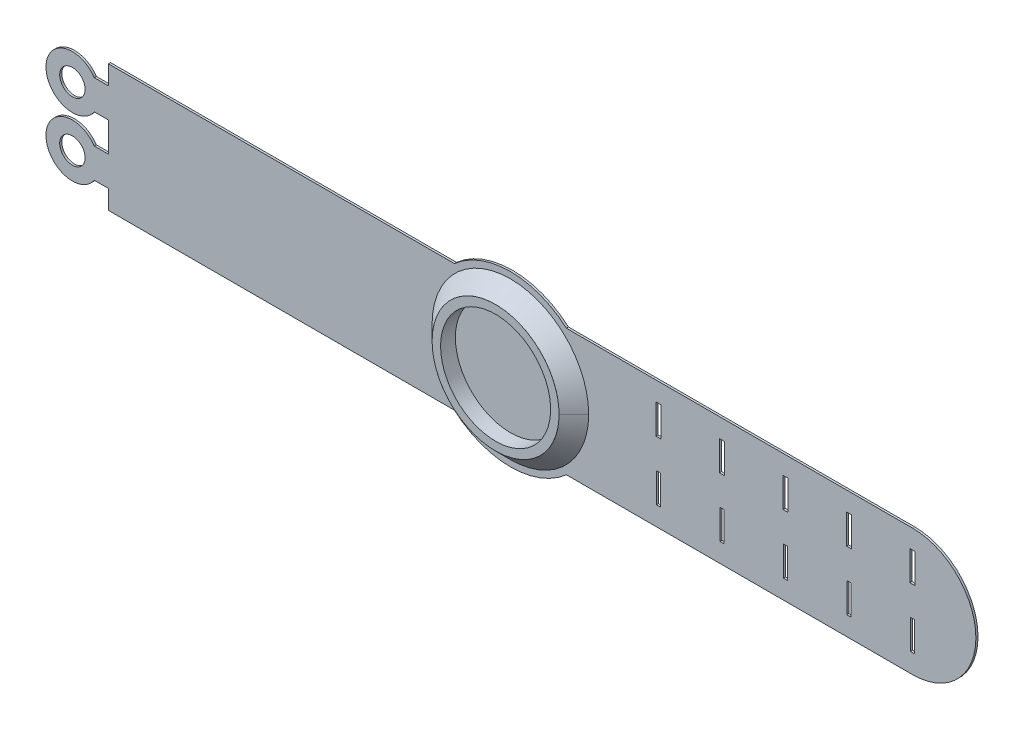
SolidWorks part; units mm, degrees
ref_plane "Спереди" through (0, 0, 0) normal (0, 0, 1) x (1, 0, 0)
ref_plane "Сверху" through (0, 0, 0) normal (0, 1, 0) x (1, 0, 0)
ref_plane "Справа" through (0, 0, 0) normal (1, 0, 0) x (0, 0, -1)
sketch "Эскиз1" plane through (0, 0, 0) normal (0, 0, 1) x (1, 0, 0)
  line L0 (13.2288, 15) -> (95, 15)
  line L1 (-95, 15) -> (-13.2288, 15)
  line L3 (-95, -15) -> (-13.2288, -15)
  line L5 (-95, 15) -> (95, -15) construction
  line L6 (-95, -15) -> (95, 15) construction
  line L7 (13.2288, -15) -> (95, -15)
  line L8 (-95, 15) -> (-95, -15)
  line L9 (80.6, 10.5) -> (80.6, 3.5)
  line L10 (-98.3219, 10.5) -> (-95, 10.5)
  line L12 (-98.3219, 3.5) -> (-95, 3.5)
  line L13 (-95, 10.5) -> (-95, 3.5)
  line L14 (-99.9506, 11.201) -> (-95, 3.5) construction
  line L15 (-99.0084, 4.2647) -> (-95, 10.5) construction
  line L16 (-98.3219, -3.5) -> (-95, -3.5)
  line L18 (-98.3219, -10.5) -> (-95, -10.5)
  line L19 (-95, -3.5) -> (-95, -10.5)
  line L20 (-99.0084, -4.2647) -> (-95, -10.5) construction
  line L21 (-99.9506, -11.201) -> (-95, -3.5) construction
  line L22 (95.6, 10.5) -> (94.4, 10.5)
  line L23 (95.6, 10.5) -> (95.6, 3.5)
  line L24 (95.6, 3.5) -> (94.4, 3.5)
  line L25 (94.4, 10.5) -> (94.4, 3.5)
  line L26 (95.6, 10.5) -> (94.4, 3.5) construction
  line L27 (95.6, 3.5) -> (94.4, 10.5) construction
  line L28 (95.5, -3.5) -> (94.5, -3.5)
  line L29 (95.5, -3.5) -> (95.5, -10.5)
  line L30 (95.5, -10.5) -> (94.5, -10.5)
  line L31 (94.5, -3.5) -> (94.5, -10.5)
  line L32 (95.5, -3.5) -> (94.5, -10.5) construction
  line L33 (95.5, -10.5) -> (94.5, -3.5) construction
  line L34 (80.6, 10.5) -> (79.4, 10.5)
  line L35 (79.4, 10.5) -> (79.4, 3.5)
  line L36 (80.6, 3.5) -> (79.4, 3.5)
  line L37 (80.5, -3.5) -> (79.5, -3.5)
  line L38 (80.5, -3.5) -> (80.5, -10.5)
  line L39 (79.5, -3.5) -> (79.5, -10.5)
  line L40 (80.5, -10.5) -> (79.5, -10.5)
  line L41 (65.6, 10.5) -> (65.6, 3.5)
  line L42 (65.6, 10.5) -> (64.4, 10.5)
  line L43 (64.4, 10.5) -> (64.4, 3.5)
  line L44 (65.6, 3.5) -> (64.4, 3.5)
  line L45 (65.5, -3.5) -> (64.5, -3.5)
  line L46 (65.5, -3.5) -> (65.5, -10.5)
  line L47 (64.5, -3.5) -> (64.5, -10.5)
  line L48 (65.5, -10.5) -> (64.5, -10.5)
  line L49 (50.6, 10.5) -> (50.6, 3.5)
  line L50 (50.6, 10.5) -> (49.4, 10.5)
  line L51 (49.4, 10.5) -> (49.4, 3.5)
  line L52 (50.6, 3.5) -> (49.4, 3.5)
  line L53 (50.5, -3.5) -> (49.5, -3.5)
  line L54 (50.5, -3.5) -> (50.5, -10.5)
  line L55 (49.5, -3.5) -> (49.5, -10.5)
  line L56 (50.5, -10.5) -> (49.5, -10.5)
  line L57 (34.5, -3.5) -> (34.5, -10.5)
  line L58 (35.5, -3.5) -> (35.5, -10.5)
  line L59 (35.5, -10.5) -> (34.5, -10.5)
  line L60 (35.5, -3.5) -> (34.5, -3.5)
  line L61 (35.6, 3.5) -> (34.4, 3.5)
  line L62 (35.6, 10.5) -> (35.6, 3.5)
  line L63 (34.4, 10.5) -> (34.4, 3.5)
  line L64 (35.6, 10.5) -> (34.4, 10.5)
  line L73 (20.5, -3.5) -> (20.5, -10.5) [skipped]
  line L74 (20.5, -10.5) -> (19.5, -10.5) [skipped]
  line L75 (20.5, -3.5) -> (19.5, -3.5) [skipped]
  line L76 (19.4, 10.5) -> (19.4, 3.5) [skipped]
  line L77 (20.6, 10.5) -> (20.6, 3.5) [skipped]
  line L78 (20.6, 3.5) -> (19.4, 3.5) [skipped]
  line L79 (20.6, 10.5) -> (19.4, 10.5) [skipped]
  line L80 (19.5, -3.5) -> (19.5, -10.5) [skipped]
  arc A0 (13.2288, 15) -> (-13.2288, 15) centre (0, 0) ccw
  arc A1 (95, -15) -> (95, 15) centre (95, 0) ccw
  arc A2 (-13.2288, -15) -> (13.2288, -15) centre (0, 0) ccw
  arc A3 (-98.3219, 10.5) -> (-98.3219, 3.5) centre (-103.5, 7) ccw
  arc A4 (-98.3219, -3.5) -> (-98.3219, -10.5) centre (-103.5, -7) ccw
  circle A5 centre (-103.5, 7) radius 3
  circle A6 centre (-103.5, -7) radius 3
  point P0 (0, 0)
  point P11 (-97.25, 7)
  point P17 (-97.25, -7)
  point P23 (-96.661, 3.5)
  point P26 (-96.661, -3.5)
  point P32 (95, 7)
  point P37 (95, -7)
  dimension "D3" = 40
  dimension "D4" = 20
  dimension "D5" = 0
  dimension "D6" = 5
  dimension "D12" = 12.5
  dimension "D13" = 12.5
  dimension "D16" = 6
  dimension "D17" = 6
  dimension "D18" = 8.5
  dimension "D21" = 8.5
  dimension "D1" = 190
  dimension "D2" = 30
  dimension "D7" = 5
  dimension "D8" = 8
  dimension "D9" = 8
  dimension "D10" = 7
  dimension "D11" = 7
  dimension "D14" = 8
  dimension "D15" = 8
  dimension "D19" = 4.5
  dimension "D20" = 11.5
  dimension "D22" = 4.5
  dimension "D23" = 18.5
  dimension "D24" = 8
  dimension "D25" = 8
  dimension "D26" = 7
  dimension "D27" = 7
  dimension "D28" = 1.2
  dimension "D29" = 1
  dimension "D31" = 14.4
  dimension "D33" = 14
  dimension "D30" = 4
  dimension "D32" = 3
extrude "Бобышка-Вытянуть2" add sketch "Эскиз1" along normal blind 0.5 contours L10 A3 L12 L8 A5 | L3 A2 L7 A1 L0 A0 L1 L8 L54 L56 L55 L53 L49 L52 L51 L50 L46 L48 L47 L45 L41 L44 L43 L42 L38 L40 L39 L37 L9 L36 L35 L34 L25 L22 L23 L24 L31 L28 L29 | L16 A4 L18 L8 A6
sketch "Эскиз3" plane through (0, 0, 0) normal (0, 0, -1) x (-1, 0, 0)
  circle A0 centre (0, 0) radius 13
  circle A1 centre (0, 0) radius 15
  dimension "D1" = 26
  dimension "D2" = 30
extrude "Бобышка-Вытянуть3" add sketch "Эскиз3" against normal blind 4
sketch3d "Трехмерный эскиз1"
  line L0 (15, 0, 0.5) -> (18.5, 0, 0.5)
  line L1 (15, 0, 4) -> (18.5, 0, 0.5)
  line L2 (15, 0, 4) -> (15, 0, 0.5)
  circle A0 centre (0, 0, 0.5) radius 15 construction
  circle A1 centre (0, 0, 4) radius 15 construction
  point P4 (0, 0, 15.5)
  point P9 (0, 0, -11)
  dimension "D1" = 45
sketch "Эскиз7" plane through (0, 0, 0) normal (0, 0, -1) x (-1, 0, 0)
surface "Поверхность-По траектории1"
sketch3d "Трехмерный эскиз2"
  line L0 (-15, 0, 4) -> (15, 0, 4) construction
  line L1 (0, -15, 4) -> (0, 15, 4) construction
  line L2 (-10.6066, -10.6066, 4) -> (10.6066, 10.6066, 4) construction
  line L3 (10.6066, -10.6066, 4) -> (-10.6066, 10.6066, 4) construction
  line L4 (-13.8582, -5.7403, 4) -> (13.8582, 5.7403, 4) construction
  line L5 (-5.7403, -13.8582, 4) -> (5.7403, 13.8582, 4) construction
  line L6 (-13.8582, 5.7403, 4) -> (13.8582, -5.7403, 4) construction
  line L7 (5.7403, -13.8582, 4) -> (-5.7403, 13.8582, 4) construction
  line L8 (13.8582, -5.7403, 4) -> (17.0918, -7.0796, 0.5)
  line L9 (13.8582, 5.7403, 4) -> (17.0918, 7.0796, 0.5)
  line L10 (17.0918, -7.0796, 0.5) -> (18.9395, -7.845, 0.5)
  line L11 (13.8582, -5.7403, 4) -> (15.706, -6.5056, 4)
  line L12 (15.706, -6.5056, 4) -> (18.9395, -7.845, 0.5)
  line L13 (17.0918, 7.0796, 0.5) -> (18.9395, 7.845, 0.5)
  line L14 (13.8582, 5.7403, 4) -> (15.706, 6.5056, 4)
  line L15 (15.706, 6.5056, 4) -> (18.9395, 7.845, 0.5)
  line L17 (-17.0918, -7.0796, 0.5) -> (-18.9395, -7.845, 0.5)
  line L18 (-13.8582, -5.7403, 4) -> (-17.0918, -7.0796, 0.5)
  line L19 (-15.706, -6.5056, 4) -> (-18.9395, -7.845, 0.5)
  line L20 (-17.0918, 7.0796, 0.5) -> (-18.9395, 7.845, 0.5)
  line L21 (-13.8582, 5.7403, 4) -> (-15.706, 6.5056, 4)
  line L22 (-13.8582, 5.7403, 4) -> (-17.0918, 7.0796, 0.5)
  line L23 (-15.706, 6.5056, 4) -> (-18.9395, 7.845, 0.5)
  line L24 (-13.8582, -5.7403, 4) -> (-15.706, -6.5056, 4)
  circle A0 centre (0, 0, 4) radius 15 construction
  arc A1 (-15, 0, 4) -> (15, 0, 4) centre (0, 0, 4) ccw construction
  arc A2 (15, 0, 4) -> (-15, 0, 4) centre (0, 0, 4) ccw construction
  arc A3 (-18.5, 0, 0.5) -> (18.5, 0, 0.5) centre (0, 0, 0.5) ccw construction
  arc A4 (18.5, 0, 0.5) -> (-18.5, 0, 0.5) centre (0, 0, 0.5) ccw construction
  arc A5 (-15.706, 6.5056, 4) -> (-15.706, -6.5056, 4) centre (0, 0, 4) ccw
  arc A6 (15.706, -6.5056, 4) -> (15.706, 6.5056, 4) centre (0, 0, 4) ccw
  point P8 (0, 0, -11)
  point P12 (0, 0, 19)
  point P16 (0, 0, 19)
  point P19 (0, 0, 4)
  point P34 (0, 0, 19)
  point P40 (0, 0, 19)
  point P52 (0, 0, 21)
  point P53 (0, 0, 21)
  dimension "D2" = 22.5
  dimension "D3" = 22.5
  dimension "D4" = 22.5
  dimension "D5" = 22.5
  dimension "D6" = 22.5
  dimension "D7" = 135
  dimension "D8" = 135
  dimension "D9" = 2
sketch "Эскиз24" plane through (0, 0, 0.5) normal (0, 0, 1) x (1, 0, 0)
  line L0 (0, 0) -> (-17.0918, 7.0796)
sketch3d "Трехмерный эскиз3"
  line L0 (-13.8582, 5.7403, 4) -> (-13.8582, 5.7403, 0.5)
  line L1 (0, 0, 0.5) -> (-17.0918, 7.0796, 0.5) construction
